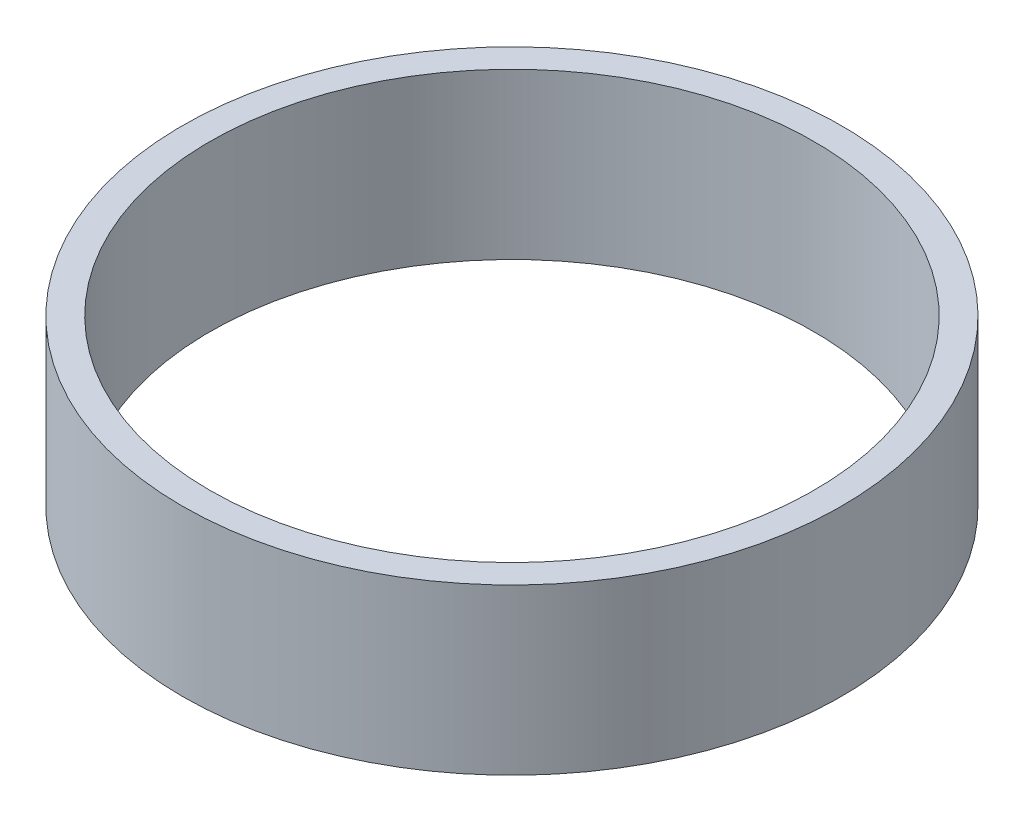
SolidWorks part; units mm, degrees
ref_plane "Front" through (0, 0, 0) normal (0, 0, 1) x (1, 0, 0)
ref_plane "Top" through (0, 0, 0) normal (0, 1, 0) x (1, 0, 0)
ref_plane "Right" through (0, 0, 0) normal (1, 0, 0) x (0, 0, -1)
sketch "草圖1" plane through (0, 0, 0) normal (0, 1, 0) x (1, 0, 0)
  circle A0 centre (0, 0) radius 60
  dimension "D1" = 120
extrude "填料-伸長1" add sketch "草圖1" along normal blind 30
shell "薄殼1" thickness 5
